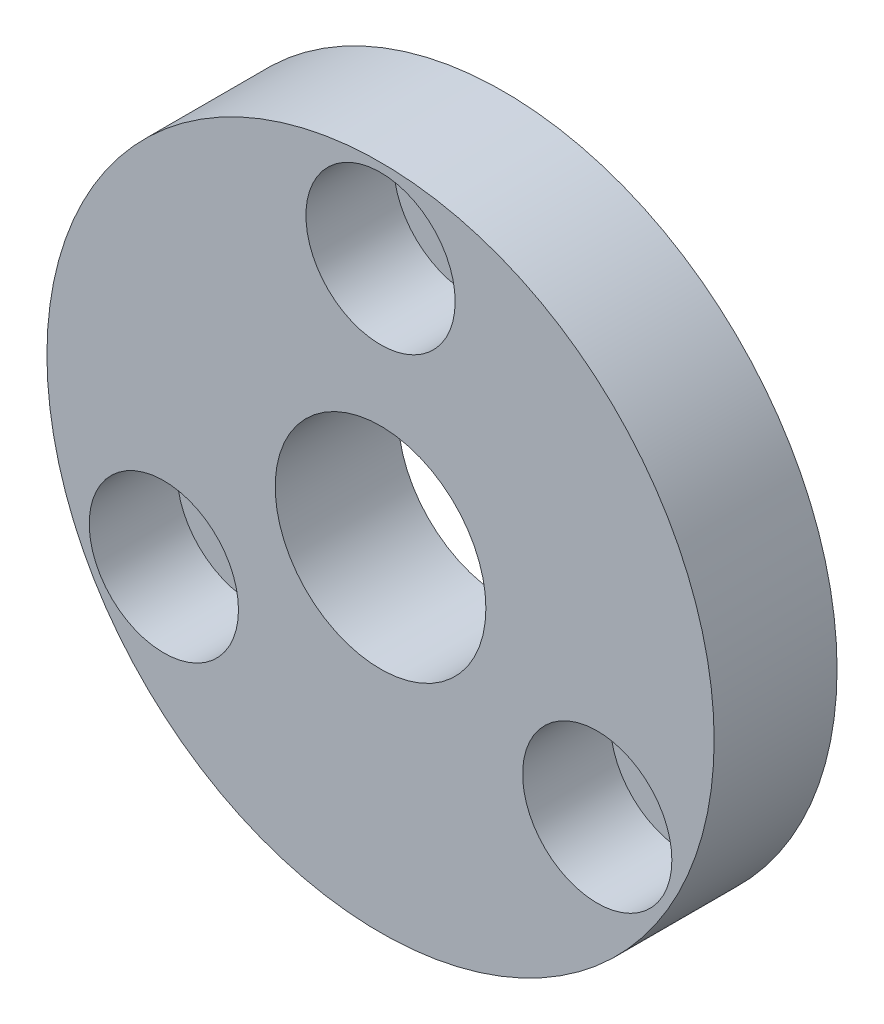
SolidWorks part; units mm, degrees
ref_plane "Plan de face" through (0, 0, 0) normal (0, 0, 1) x (1, 0, 0)
ref_plane "Plan de dessus" through (0, 0, 0) normal (0, 1, 0) x (1, 0, 0)
ref_plane "Plan de droite" through (0, 0, 0) normal (1, 0, 0) x (0, 0, -1)
sketch "Esquisse1" plane through (0, 0, 0) normal (0, 0, 1) x (1, 0, 0)
  circle A0 centre (0, 0) radius 19
  circle A1 centre (0, 0) radius 6
  circle A2 centre (12.3409, -7.125) radius 2.5
  circle A3 centre (0, 14.25) radius 2.5
  circle A4 centre (-12.3409, -7.125) radius 2.5
  dimension "D1" = 14.25
  dimension "D2" = 38
extrude "Extrusion1" add sketch "Esquisse1" along normal blind 7
sketch "Esquisse2" plane through (0, 0, 7) normal (0, 0, 1) x (1, 0, 0)
  circle A0 centre (0, 14.25) radius 4.25
  circle A1 centre (-12.3409, -7.125) radius 4.25
  circle A2 centre (12.3409, -7.125) radius 4.25
extrude "Extrusion2" cut sketch "Esquisse2" against normal blind 5
